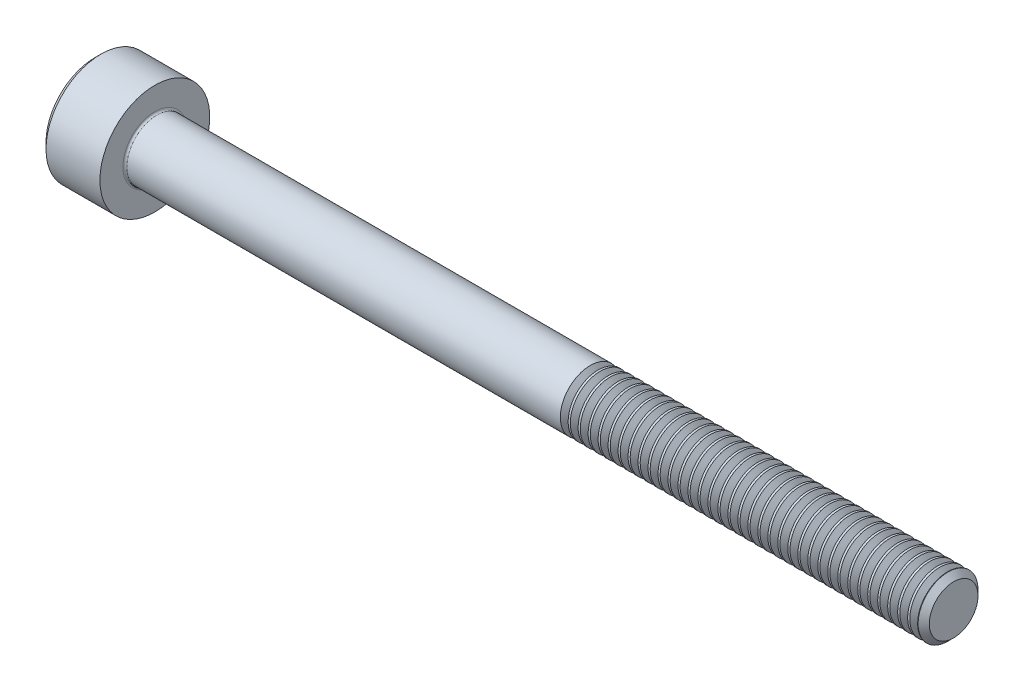
SolidWorks part; units mm, degrees
ref_plane "Plane1" through (0, 0, 0) normal (0, 0, 1) x (1, 0, 0)
ref_plane "Plane2" through (0, 0, 0) normal (0, 1, 0) x (1, 0, 0)
ref_plane "Plane3" through (0, 0, 0) normal (1, 0, 0) x (0, 0, -1)
sketch "BodySke" plane through (0, 0, 0) normal (0, 0, 1) x (1, 0, 0)
  line L0 (0, 0) -> (0, 2.45)
  line L1 (0.3, 2.75) -> (3, 2.75)
  line L2 (3, 2.75) -> (3, 1.5)
  line L3 (3, 1.5) -> (42.7195, 1.5)
  line L4 (43, 1.2195) -> (43, 0)
  line L5 (43, 0) -> (0, 0)
  line L6 (-31.75, 0) -> (127, 0) construction
  line L7 (0, 2.45) -> (0.3, 2.75)
  line L8 (43, 1.2195) -> (42.7195, 1.5)
  line L9 (0, -2.45) -> (0.3, -2.75) construction
  line L10 (43, -1.2195) -> (42.7195, -1.5) construction
  line L11 (3.5, 9.525) -> (3.5, 3.175) construction
  line L12 (25, 9.525) -> (25, 3.175) construction
  line L13 (-7, 9.525) -> (-7, 3.175) construction
  dimension "Diameter" = 3
  dimension "Head_ht" = 3
  dimension "Length" = 40
  dimension "Body_ch_ang" = 45
  dimension "Head_dia" = 5.5
  dimension "Head_ch_ang" = 45
  dimension "Minor_dia" = 2.439
  dimension "Advance" = 0.5
  dimension "Thread_nom" = 18
  dimension "Thread_length" = 50
  dimension "Head_ch_ht" = 0.3
revolve "Base-Revolve" add sketch "BodySke"
cosmetic thread "ThreadCosmetic" [suppressed]
fillet "Fillet1" radius 0.1 1 edges at (3, 0, 1.5)
sketch "Sketch2" plane through (0, 0, 0) normal (0, 0, 1) x (1, 0, 0)
  line L0 (0, 1.28) -> (1.3, 1.28)
  line L1 (1.3, 1.28) -> (2.039, 0)
  line L2 (-31.75, 0) -> (127, 0) construction
  line L3 (2.039, 0) -> (0, 0)
  line L4 (0, 0) -> (0, 1.28)
  line L5 (0, 2.45) -> (0, -2.45) construction
  line L6 (0, 0) -> (47.625, 0) construction
  line L7 (3, -2.75) -> (3, 2.75) construction
  dimension "D1" = 1.28
  dimension "D2" = 60
  dimension "Wall_thickness" = 1.7
revolve "Hex-PreBroach" cut sketch "Sketch2" angle 360 about L6
sketch "Sketch3" plane through (0, 0, 0) normal (-1, 0, 0) x (0, 0.5, 0.866)
  line L0 (0.739, 1.28) -> (-0.739, 1.28)
  line L1 (-0.739, 1.28) -> (-1.478, 0)
  line L2 (0.739, 1.28) -> (1.478, 0)
  line L3 (0.739, -1.28) -> (1.478, 0)
  line L4 (0.739, -1.28) -> (-0.739, -1.28)
  line L5 (-0.739, -1.28) -> (-1.478, 0)
  dimension "D1" = 1.28
  dimension "D2" = 1.28
  dimension "Hex_size" = 2.56
extrude "Hex" cut sketch "Sketch3" against normal blind 1.3
sketch "Sketch4" plane through (0, 0, 0) normal (-1, 0, 0) x (0, 0, 1)
  line L0 (0, 0) -> (1.4605, 0)
  line L1 (0, 0) -> (6.1484, 3.5498) construction
  line L2 (0, 0) -> (0.7302, 1.2648)
  line L3 (1.2009, 0.3267) -> (1.3933, 0.4378)
  line L4 (0.8834, 0.8767) -> (1.0758, 0.9877)
  arc A0 (1.2009, 0.3267) -> (0.8834, 0.8767) centre (0, 0) ccw
  arc A1 (1.4605, 0) -> (1.3933, 0.4378) centre (0, 0) ccw
  arc A2 (0.7302, 1.2648) -> (1.0758, 0.9877) centre (0, 0) cw
  dimension "D1" = 30
  dimension "Spline_n_dim" = 2.4892
  dimension "Spline_m_dim" = 2.921
  dimension "D2" = 60
  dimension "D3" = 0.3175
  dimension "Spline_p_dim" = 0.635
extrude "Spline" [suppressed] cut sketch "Sketch4" against normal blind 1.3
pattern_circular "CirPattern1" [suppressed] count 6 every 60
sketch "Sketch5" plane through (0, 0, 0) normal (0, 0, 1) x (1, 0, 0)
  line L0 (-31.75, 0) -> (127, 0) construction
  line L2 (0, 2.45) -> (0, -2.45) construction
  circle A0 centre (1.2, 0) radius 0.475
  dimension "Drilled_hole_dia" = 0.95
  dimension "Drilled_hole_loc" = 1.2
extrude "Hole" [suppressed] cut sketch "Sketch5" against normal through all and the other way through all
pattern_circular "Drilled-4" [suppressed] count 2 every 60
pattern_circular "Drilled-6" [suppressed] count 3 every 60
sketch "ThdSchSke" plane through (0, 0, 0) normal (0, 0, 1) x (1, 0, 0)
  line L0 (25, -1.2195) -> (24.8036, -1.5)
  line L1 (25, -1.2195) -> (25.1964, -1.5)
  line L2 (25.1964, -1.5) -> (25.1964, -1.875)
  line L3 (-3.175, 0) -> (5.1513, 0) construction
  line L5 (25.1964, -1.875) -> (24.8036, -1.875)
  line L6 (24.8036, -1.875) -> (24.8036, -1.5)
  line L7 (0, 2.45) -> (0, -2.45) construction
  dimension "Thread_minor" = 2.439
  dimension "Diameter" = 3
  dimension "Start" = 25
  dimension "SideAngle" = 55
  dimension "VeeAngle" = 70
  dimension "Overcut" = 3.75
revolve "ThreadSchematic" cut sketch "ThdSchSke" angle 360 about L3
pattern_linear "ThdSchPat" count 36 spacing 0.5 along (1, 0, 0) of "ThreadSchematic"
equation "\"D2@Sketch3\" = \"Hex_size@Sketch3\" / 2"
equation "\"D1@Sketch3\" = \"Hex_size@Sketch3\" / 2"
equation "\"D1@Sketch2\" = \"Hex_size@Sketch3\" / 2"
equation "\"D3@Sketch4\" = \"Spline_p_dim@Sketch4\" / 2"
equation "\"Thread_minor@ThreadCosmetic\"  =  \"Minor_dia@BodySke\""
equation "\"D2@CirPattern1\" = 360 / \"Num_teeth@CirPattern1\""
equation "\"Wall_thickness@Sketch2\" = \"Head_ht@BodySke\" - \"Key_eng@Hex\""
equation "\"Thread_length@ThreadCosmetic\" = ((sgn( (\"Length@BodySke\" - \"Advance@BodySke\" ) - \"Thread_nom@BodySke\" )-1)*( (\"Length@BodySke\" - \"Advance@BodySke\" ) - \"Thread_nom@BodySke\" ))/-2+ \"Thread_nom@BodySke\""
equation "\"Thread_minor@ThdSchSke\" = \"Minor_dia@BodySke\""
equation "\"Diameter@ThdSchSke\" = \"Diameter@BodySke\""
equation "\"Overcut@ThdSchSke\" = \"Diameter@BodySke\" * 1.25"
equation "\"Start@ThdSchSke\" = \"Head_ht@BodySke\" + \"Length@BodySke\" - \"Thread_length@ThreadCosmetic\"  '---Non-countersunk---"
equation "\"Num_threads@ThdSchPat\" = int( \"Thread_length@ThreadCosmetic\" / \"Advance@BodySke\" + 0.999 )  + 1"
equation "\"Advance@ThdSchPat\" = \"Thread_length@ThreadCosmetic\" /  (\"Num_threads@ThdSchPat\" - 1) 'relax it"
equation "\"Num_threads@ThdSchPat\" = \"Num_threads@ThdSchPat\" - sgn( \"Num_threads@ThdSchPat\" - 1) '---chamfered tips only---"
